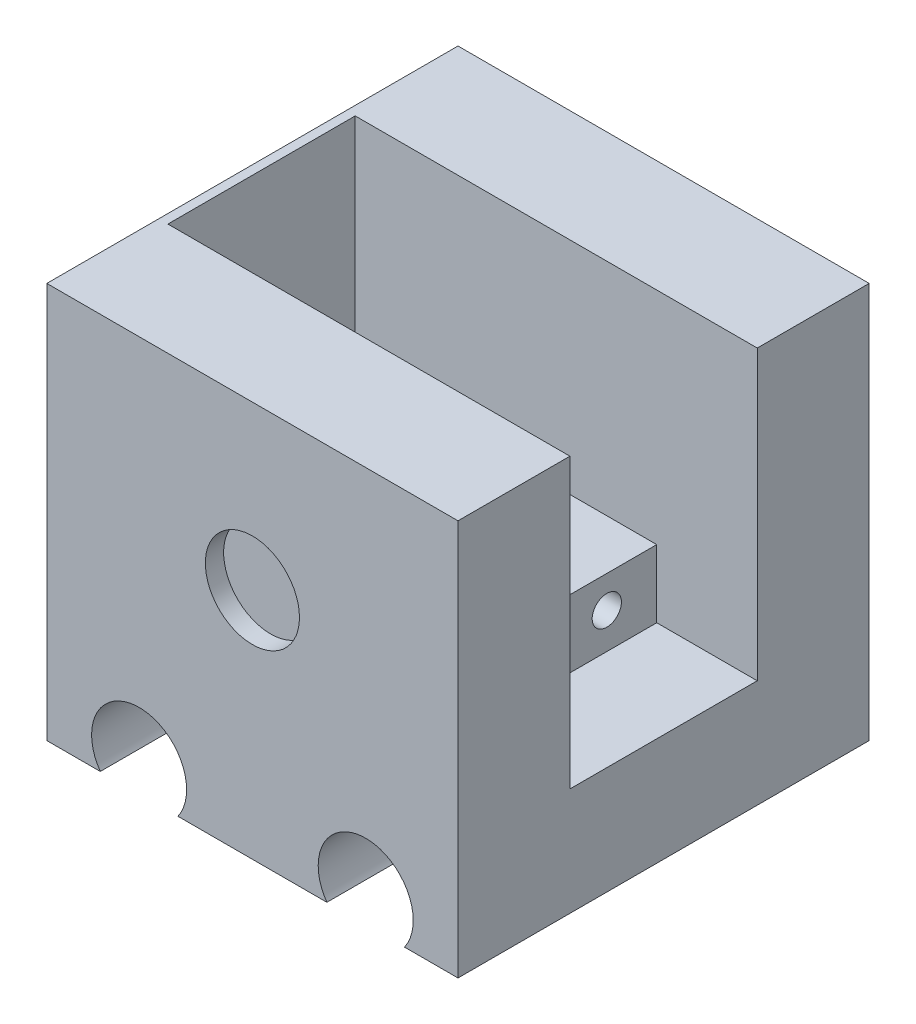
SolidWorks part; units mm, degrees
ref_plane "Front Plane" through (0, 0, 0) normal (0, 0, 1) x (1, 0, 0)
ref_plane "Top Plane" through (0, 0, 0) normal (0, 1, 0) x (1, 0, 0)
ref_plane "Right Plane" through (0, 0, 0) normal (1, 0, 0) x (0, 0, -1)
sketch "Sketch1" plane through (0, 0, 0) normal (0, 0, 1) x (1, 0, 0)
  line L1 (-14.2634, 22.0982) -> (30.7366, 22.0982)
  line L2 (-14.2634, 22.0982) -> (-14.2634, -27.9018)
  line L3 (-14.2634, -27.9018) -> (30.7366, -27.9018)
  line L4 (30.7366, 22.0982) -> (30.7366, -27.9018)
  dimension "D1" = 50
  dimension "D2" = 45
extrude "Boss-Extrude1" add sketch "Sketch1" along normal blind 45
sketch "Sketch2" plane through (0, 0, 45) normal (0, 0, 1) x (1, 0, 0)
  line L0 (-14.2634, -27.9018) -> (30.7366, -27.9018) construction
  line L1 (-14.2634, 22.0982) -> (-14.2634, -27.9018) construction
  circle A0 centre (-4.1634, -24.9018) radius 5.2
  circle A1 centre (20.6366, -24.9018) radius 5.2
  dimension "D1" = 3
  dimension "D3" = 10.1
  dimension "D2" = 2
extrude "Cut-Extrude1" cut sketch "Sketch2" against normal blind 45
sketch "Sketch9" plane through (0, 0, 45) normal (0, 0, 1) x (1, 0, 0)
  line L0 (8.2366, 22.0982) -> (8.2366, -2.4018) construction
  line L1 (30.7366, 22.0982) -> (-14.2634, 22.0982) construction
  circle A0 centre (8.2366, -2.4018) radius 5.15
  dimension "D1" = 24.5
extrude "Cut-Extrude6" cut sketch "Sketch9" against normal blind 2
sketch "Sketch10" plane through (0, 0, 0) normal (0, 0, -1) x (-1, 0, 0)
  line L0 (-8.2366, 22.0982) -> (-8.2366, -2.4018) construction
  line L1 (-30.7366, 22.0982) -> (14.2634, 22.0982) construction
  circle A0 centre (-8.2366, -2.4018) radius 5.15
  dimension "D1" = 24.5
extrude "Cut-Extrude7" cut sketch "Sketch10" against normal blind 2
sketch "Sketch12" plane through (-14.2634, 0, 0) normal (-1, 0, 0) x (0, 0, 1)
  line L0 (22.5, 22.0982) -> (22.5, -7.2504) construction
  line L1 (45, 22.0982) -> (0, 22.0982) construction
  line L2 (0, -16.4263) -> (45, -16.4263) construction
  line L3 (0, 22.0982) -> (0, -27.9018) construction
  line L4 (45, 22.0982) -> (45, -27.9018) construction
  circle A0 centre (22.5, 0) radius 12.7
  dimension "D1" = 25.4
extrude "Cut-Extrude8" cut sketch "Sketch12" against normal blind 46
sketch "Sketch13" plane through (-14.2634, 0, 0) normal (-1, 0, 0) x (0, 0, 1)
  line L0 (45, 22.0982) -> (45, -27.9018) construction
  line L1 (0, 22.0982) -> (45, 22.0982)
  line L2 (0, 22.0982) -> (0, 15.4307)
  line L3 (0, 15.4307) -> (45, 15.4307)
  line L4 (45, 22.0982) -> (45, 15.4307)
extrude "Cut-Extrude9" cut sketch "Sketch13" against normal blind 46
sketch "Sketch16" plane through (30.7366, 0, 0) normal (1, 0, 0) x (0, 0, -1)
  circle A0 centre (-22.5, 0) radius 13.25
  circle A1 centre (-22.5, 0) radius 3.75
extrude "Boss-Extrude3" add sketch "Sketch16" against normal blind 2
sketch "Sketch19" plane through (30.7366, 0, 0) normal (1, 0, 0) x (0, 0, -1)
  circle A0 centre (-22.5, 0) radius 3.75
sketch "Sketch20" plane through (-14.2634, 0, 0) normal (-1, 0, 0) x (0, 0, 1)
  circle A0 centre (22.5, 0) radius 12.7
extrude "Boss-Extrude4" add sketch "Sketch20" against normal blind 45
sketch "Sketch21" plane through (30.7366, 0, 0) normal (1, 0, 0) x (0, 0, -1)
  line L0 (-45, -27.9018) -> (-45, 15.4307) construction
  line L1 (-32.75, -16.5) -> (-12.25, -16.5)
  line L2 (-32.75, -16.5) -> (-32.75, 24)
  line L3 (-32.75, 24) -> (-12.25, 24)
  line L4 (-12.25, -16.5) -> (-12.25, 24)
  dimension "D1" = 40.5
  dimension "D2" = 20.5
  dimension "D3" = 12.25
  dimension "D4" = 16.5
extrude "Cut-Extrude10" cut sketch "Sketch21" against normal blind 44
sketch "Sketch22" plane through (30.7366, 0, 0) normal (1, 0, 0) x (0, 0, -1)
  line L0 (-32.5, -8.699) -> (-12.5, -8.699)
  line L4 (-32.75, 15.4307) -> (-32.75, -16.5) construction
  line L5 (-32.5, -8.699) -> (-32.75, -8.699)
  line L6 (-32.75, -8.699) -> (-32.75, -16.5)
  line L7 (-32.75, -16.5) -> (-12.25, -16.5)
  line L8 (-12.25, -16.5) -> (-12.25, -8.699)
  line L9 (-12.25, -16.5) -> (-12.25, 15.4307) construction
  line L10 (-12.25, -8.699) -> (-12.5, -8.699)
  circle A0 centre (-27.2153, -10.949) radius 2.15
  circle A1 centre (-17.7153, -10.949) radius 2.15
extrude "Boss-Extrude5" add sketch "Sketch22" against normal blind 44
sketch "Sketch26" plane through (0, -8.699, 0) normal (0, 1, 0) x (1, 0, 0)
  line L0 (-13.2634, -12.25) -> (-13.2634, -32.75) construction
  line L1 (-13.2634, -18.5) -> (-8.1363, -18.5)
  line L2 (-13.2634, -18.5) -> (-13.2634, -26.5)
  line L3 (-13.2634, -26.5) -> (-8.1363, -26.5)
  line L4 (-8.1363, -18.5) -> (-8.1363, -26.5)
  line L5 (-13.2634, -12.25) -> (30.7366, -12.25) construction
  dimension "D1" = 8
  dimension "D2" = 6.25
extrude "Cut-Extrude16" cut sketch "Sketch26" against normal blind 7
sketch "Sketch27" plane through (-13.2634, 0, 0) normal (1, 0, 0) x (0, 0, -1)
  line L0 (-18.5, -15.699) -> (-18.5, -12.9507) construction
  line L1 (-26.5, -8.699) -> (-18.5, -8.699)
  line L2 (-26.5, -8.699) -> (-26.5, -15.699)
  line L3 (-26.5, -15.699) -> (-18.5, -15.699)
  line L4 (-18.5, -8.699) -> (-18.5, -15.699)
  line L5 (-18.5, -15.699) -> (-26.5, -15.699) construction
sketch "Sketch28" plane through (30.7366, 0, 0) normal (1, 0, 0) x (0, 0, -1)
  circle A0 centre (-27.2153, -10.949) radius 2.15
  circle A1 centre (-17.7153, -10.949) radius 2.15
extrude "Boss-Extrude6" add sketch "Sketch28" against normal blind 44
sketch "Sketch29" plane through (30.7366, 0, 0) normal (1, 0, 0) x (0, 0, -1)
  line L1 (-12.25, -8.699) -> (-32.75, -8.699) construction
  circle A0 centre (-27.2153, -12.199) radius 2.15
  circle A1 centre (-17.7153, -12.199) radius 2.15
  dimension "D1" = 3.5
  dimension "D2" = 3.5
extrude "Cut-Extrude18" cut sketch "Sketch29" against normal blind 10
sketch "Sketch30" plane through (-13.2634, 0, 0) normal (1, 0, 0) x (0, 0, -1)
  line L1 (-26.5, -8.699) -> (-18.5, -8.699)
  line L2 (-26.5, -8.699) -> (-26.5, -15.699)
  line L3 (-26.5, -15.699) -> (-18.5, -15.699)
  line L4 (-18.5, -8.699) -> (-18.5, -15.699)
extrude "Cut-Extrude19" cut sketch "Sketch30" against normal blind 7 and the other way blind 7
sketch "Sketch31" plane through (30.7366, 0, 0) normal (1, 0, 0) x (0, 0, -1)
  line L1 (-32.75, -8.699) -> (-12.25, -8.699)
  line L2 (-32.75, -8.699) -> (-32.75, -16.1069)
  line L3 (-32.75, -16.1069) -> (-12.25, -16.1069)
  line L4 (-12.25, -8.699) -> (-12.25, -16.1069)
extrude "Cut-Extrude20" cut sketch "Sketch31" against normal blind 11
sketch "Sketch32" plane through (-13.2634, 0, 0) normal (1, 0, 0) x (0, 0, -1)
  line L1 (-27, -8.699) -> (-18, -8.699)
  line L2 (-27, -8.699) -> (-27, -3.6527)
  line L3 (-27, -3.6527) -> (-18, -3.6527)
  line L4 (-18, -8.699) -> (-18, -3.6527)
  line L5 (-32.75, 15.4307) -> (-32.75, -8.699) construction
  dimension "D1" = 9
  dimension "D2" = 5.75
extrude "Cut-Extrude21" cut sketch "Sketch32" against normal blind 14
sketch "Sketch33" plane through (0, -8.699, 0) normal (0, 1, 0) x (1, 0, 0)
  line L0 (-14.2634, -45) -> (-14.2634, 0) construction
  line L1 (-14.2634, -18) -> (-6.1754, -18)
  line L2 (-14.2634, -18) -> (-14.2634, -27)
  line L3 (-14.2634, -27) -> (-6.1754, -27)
  line L4 (-6.1754, -18) -> (-6.1754, -27)
  dimension "D1" = 9
extrude "Cut-Extrude22" cut sketch "Sketch33" against normal blind 7
sketch "Sketch34" plane through (19.7366, 0, 0) normal (1, 0, 0) x (0, 0, -1)
  circle A0 centre (-27.2153, -12.199) radius 1.6
  circle A1 centre (-17.7153, -12.199) radius 1.6
extrude "Cut-Extrude23" cut sketch "Sketch34" against normal blind 10
sketch "Sketch35" plane through (0, -8.699, 0) normal (0, 1, 0) x (1, 0, 0)
  line L1 (-6.1754, -18) -> (-1.1754, -18)
  line L2 (-6.1754, -18) -> (-6.1754, -27)
  line L3 (-6.1754, -27) -> (-1.1754, -27)
  line L4 (-1.1754, -18) -> (-1.1754, -27)
  dimension "D1" = 5
extrude "Cut-Extrude24" cut sketch "Sketch35" against normal blind 7
